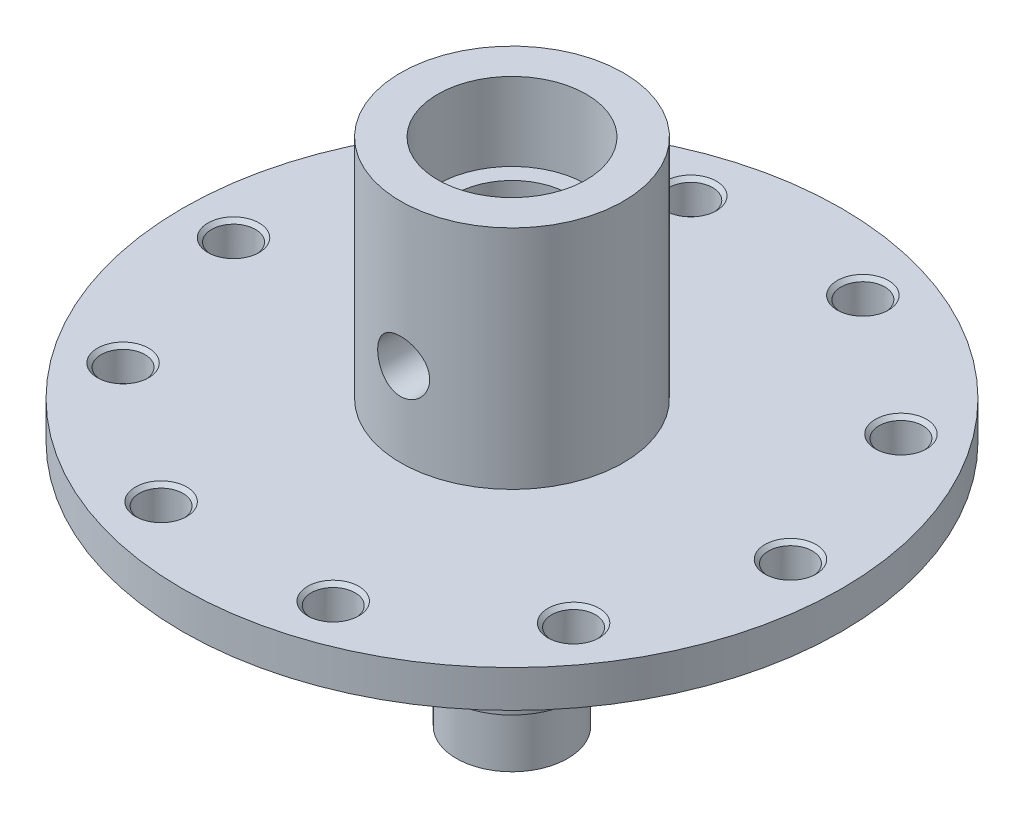
SolidWorks part; units mm, degrees
material "Inconel 718"
ref_plane "Front Plane" through (0, 0, 0) normal (0, 0, 1) x (1, 0, 0)
ref_plane "Top Plane" through (0, 0, 0) normal (0, 1, 0) x (1, 0, 0)
ref_plane "Right Plane" through (0, 0, 0) normal (1, 0, 0) x (0, 0, -1)
sketch "Sketch1" plane through (0, 0, 0) normal (0, 0, 1) x (1, 0, 0)
  line L0 (0, 9.944) -> (0, 47.3951) construction
  line L1 (0, 25.4) -> (0, -33.766)
  line L2 (0, 25.4) -> (8.89, 25.4)
  line L3 (8.89, 25.4) -> (10.16, 25.4)
  line L5 (15.24, 36.068) -> (15.24, 5.08)
  line L6 (15.24, 5.08) -> (45.085, 5.08)
  line L7 (45.085, 5.08) -> (45.085, 0)
  line L8 (45.085, 0) -> (9.525, 0)
  line L9 (8.89, 25.4) -> (8.89, -12.8295) construction
  line L10 (0, -33.766) -> (7.62, -33.766)
  line L11 (7.62, -33.766) -> (7.62, -26.146)
  line L12 (7.62, -26.146) -> (8.89, -26.146)
  line L13 (8.89, -26.146) -> (8.89, -6.35)
  line L14 (9.525, 0) -> (9.525, -6.35)
  line L15 (9.525, -6.35) -> (8.89, -6.35)
  line L18 (15.24, 36.068) -> (10.16, 36.068)
  line L19 (10.16, 25.4) -> (10.16, 36.068)
  dimension "D1" = 25.4
  dimension "D2" = 10.668
  dimension "D3" = 45.085
  dimension "D4" = 15.24
  dimension "D5" = 8.89
  dimension "D6" = 10.16
  dimension "D7" = 5.08
  dimension "D8" = 7.62
  dimension "D9" = 38.2295
  dimension "D10" = 8.89
  dimension "D11" = 19.796
  dimension "D12" = 7.62
  dimension "D13" = 6.35
  dimension "D14" = 0.635
revolve "Revolve1" add sketch "Sketch1" angle 360 about L0
cosmetic thread "Cosmetic Thread2" parameters "D1"=6.35, "D2"=12.6086
cosmetic thread "Cosmetic Thread3" parameters "D1"=6.35, "D2"=22.225
hole_wizard "Hole2" positions "Sketch8" profile "Sketch9" legacy
sketch "Sketch8" plane through (0, 25.4, 0) normal (0, 1, 0) x (1, 0, 0)
  point P0 (0, 0)
sketch "Sketch9" plane through (0, 25.4, 0) normal (1, 0, 0) x (0, 0, 1)
  line L0 (0, 0) -> (0, 43.047)
  line L1 (0, 43.047) -> (7.8105, 38.354)
  line L2 (7.8105, 38.354) -> (7.8105, 0)
  line L5 (7.8105, 0) -> (0, 0)
  line L10 (0, 43.047) -> (-7.8105, 38.354) construction
  line L11 (0, -6.35) -> (0, 107.95) construction
  dimension "Hole Dia." = 15.621
  dimension "Hole Depth" = 38.354
  dimension "Drill Angle" = 118
ref_plane "Plane2" through (0, 0, -15.24) normal (0, 0, -1) x (-1, 0, 0)
hole_wizard "1/16 NPT Tapped Hole1" positions "Sketch22" profile "Sketch23" size "1/16" standard "ANSI Inch"
sketch "Sketch22" plane through (0, 0, -15.24) normal (0, 0, -1) x (-1, 0, 0)
  point P0 (0, 16.51)
  dimension "D1" = 16.51
sketch "Sketch23" plane through (0, 16.51, -15.24) normal (1, 0, 0) x (0, 1, 0)
  line L0 (0, 0) -> (0, 24.8972)
  line L1 (3.0734, 23.0505) -> (0, 24.8972)
  line L2 (-3.0734, 23.0505) -> (0, 24.8972) construction
  line L3 (3.0734, 23.0505) -> (3.0734, 6.858)
  line L4 (3.0734, 6.858) -> (3.3648, 6.858)
  line L5 (3.3648, 6.858) -> (3.5701, 0)
  line L6 (-3.3648, 6.858) -> (-3.5701, 0) construction
  line L7 (3.5701, 0) -> (0, 0)
  line L8 (0, -6.35) -> (0, 107.95) construction
  line L11 (-3.0734, 6.858) -> (-3.3648, 6.858) construction
  dimension "Tap Drill Dia." = 6.1468
  dimension "Tap Drill Depth" = 23.0505
  dimension "Thread Dia." = 7.1403
  dimension "Thread Angle" = 3.43
  dimension "Thread Depth" = 6.858
  dimension "Drill Angle" = 118
mirror "Mirror1" about plane through (0, 0, 0) normal (0, 0, 1) of "1/16 NPT Tapped Hole1"
ref_plane "Plane3" through (0, 2.54, 0) normal (0, 1, 0) x (1, 0, 0)
hole_wizard "7/16 (0.4375) Dowel Hole1" positions "Sketch25" profile "Sketch26" hole size "7/16" standard "ANSI Inch" end condition through all
sketch "Sketch25" plane through (0, 2.54, 0) normal (0, 1, 0) x (1, 0, 0)
  point P0 (0, 0)
sketch "Sketch26" plane through (0, 2.54, 0) normal (1, 0, 0) x (0, 0, 1)
  line L0 (0, 0) -> (0, 36.306)
  line L1 (0, 36.306) -> (5.5562, 36.306)
  line L2 (5.5562, 36.306) -> (5.5562, 0)
  line L5 (5.5562, 0) -> (0, 0)
  line L11 (0, -6.35) -> (0, 107.95) construction
  dimension "Thru Hole Dia." = 11.1125
  dimension "Thru Hole Depth" = 36.306
hole_wizard "Hole1" positions "Sketch27" profile "Sketch28" legacy end condition up to next
sketch "Sketch27" plane through (0, 5.08, 0) normal (0, 1, 0) x (1, 0, 0)
  point P0 (-38.1, 0)
  dimension "D1" = 38.1
sketch "Sketch28" plane through (-38.1, 5.08, 0) normal (1, 0, 0) x (0, 0, 1)
  line L0 (0, 0) -> (0, 5.081)
  line L1 (0, 5.081) -> (3, 5.081)
  line L2 (3, 5.081) -> (3, 0)
  line L3 (3, 0) -> (0, 0)
  line L4 (0, 110) -> (0, -10) construction
  dimension "Diameter" = 6
  dimension "Depth" = 5.081
chamfer "Chamfer1" distance 0.508 angle 45 2 edges at (-38.1, 5.08, 3) (-38.1, 0, -3)
pattern_circular "CirPattern1" count 10 over 360 about axis through (0, 0, 0) along (0, 1, 0) of "Hole1", "Chamfer1"
